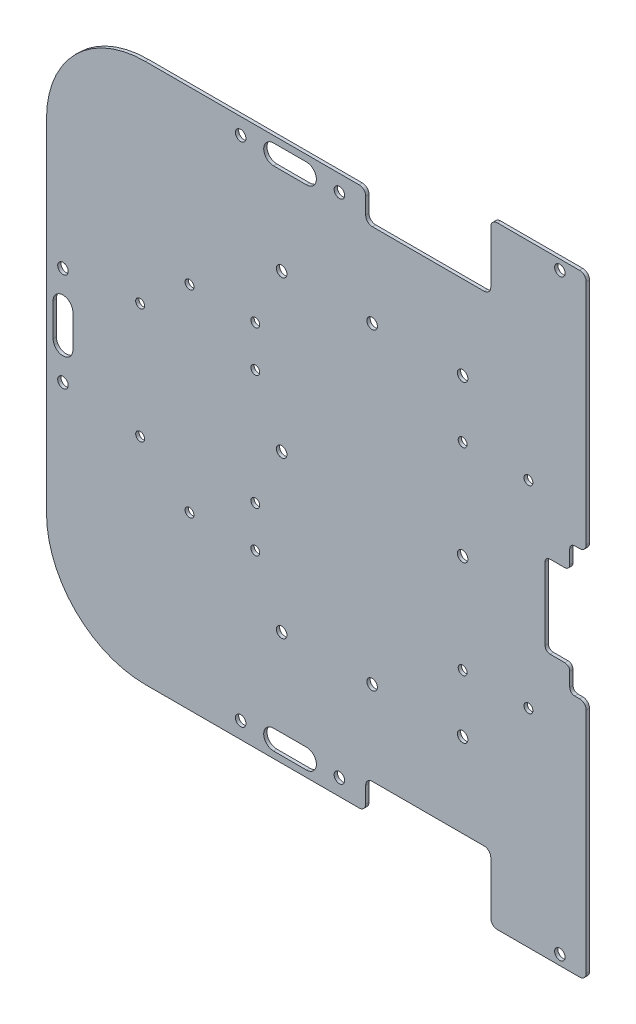
SolidWorks part; units mm, degrees
material "Thornel Mat VMA"
ref_plane "前视基准面" through (0, 0, 0) normal (0, 0, 1) x (1, 0, 0)
ref_plane "上视基准面" through (0, 0, 0) normal (0, 1, 0) x (1, 0, 0)
ref_plane "右视基准面" through (0, 0, 0) normal (1, 0, 0) x (0, 0, -1)
sketch "草图1" plane through (0, 0, 0) normal (0, 0, 1) x (1, 0, 0)
  line L1 (0, 0) -> (164, 0)
  line L2 (0, 0) -> (0, 164)
  line L3 (0, 164) -> (164, 164)
  line L4 (164, 0) -> (164, 164)
  dimension "D1" = 164
  dimension "D2" = 164
extrude "凸台-拉伸1" add sketch "草图1" along normal blind 1
fillet "圆角1" radius 30 2 edges at (0, 164, 0.5) (0, 0, 0.5)
sketch "草图2" plane through (0, 0, 1) normal (0, 0, 1) x (1, 0, 0)
  line L0 (0, 82) -> (245.8276, 82) construction
  line L1 (0, 134) -> (0, 30) construction
  line L2 (5, 77) -> (5, 87) construction
  line L3 (2, 77) -> (2, 87)
  line L4 (8, 77) -> (8, 87)
  circle A0 centre (5, 97) radius 1.6
  circle A1 centre (5, 87) radius 1.6 construction
  circle A2 centre (5, 77) radius 1.6 construction
  circle A3 centre (5, 67) radius 1.6
  arc A4 (2, 77) -> (8, 77) centre (5, 77) ccw
  arc A5 (8, 87) -> (2, 87) centre (5, 87) ccw
  point P8 (5, 82)
  dimension "D1" = 3.2
  dimension "D5" = 3
  dimension "D2" = 5
  dimension "D3" = 15
  dimension "D4" = 5
extrude "切除-拉伸1" cut sketch "草图2" against normal through all
sketch "草图3" plane through (0, 0, 1) normal (0, 0, 1) x (1, 0, 0)
  line L2 (0, 134) -> (0, 30) construction
  line L3 (59, 5) -> (69, 5) construction
  line L4 (30, 0) -> (164, 0) construction
  line L5 (0, 82) -> (216.0537, 82) construction
  line L6 (79, 5) -> (69, 5) construction
  line L7 (79, 2) -> (69, 2)
  line L8 (79, 8) -> (69, 8)
  line L9 (79, 159) -> (69, 159) construction
  line L10 (79, 162) -> (69, 162)
  line L11 (79, 156) -> (69, 156)
  circle A7 centre (59, 5) radius 1.6
  circle A8 centre (69, 5) radius 1.6 construction
  circle A9 centre (79, 5) radius 1.6 construction
  circle A10 centre (89, 5) radius 1.6
  circle A11 centre (89, 159) radius 1.6
  circle A12 centre (79, 159) radius 1.6 construction
  circle A13 centre (69, 159) radius 1.6 construction
  circle A14 centre (59, 159) radius 1.6
  arc A19 (79, 2) -> (79, 8) centre (79, 5) ccw
  arc A20 (69, 8) -> (69, 2) centre (69, 5) ccw
  arc A21 (79, 162) -> (79, 156) centre (79, 159) cw
  arc A22 (69, 156) -> (69, 162) centre (69, 159) cw
  point P24 (74, 5)
  point P26 (74, 159)
  dimension "D1" = 3.2
  dimension "D6" = 3
  dimension "D2" = 5
  dimension "D3" = 59
  dimension "D5" = 10
  dimension "D4" = 4
extrude "切除-拉伸2" cut sketch "草图3" against normal through all
sketch "草图4" plane through (0, 0, 1) normal (0, 0, 1) x (1, 0, 0)
  line L0 (0, 82) -> (207.5678, 82) construction
  line L2 (0, 134) -> (0, 30) construction
  line L4 (135, 155) -> (135, 164)
  line L5 (97, 155) -> (135, 155)
  line L6 (97, 0) -> (97, 9)
  line L7 (30, 0) -> (164, 0) construction
  line L8 (97, 9) -> (135, 9)
  line L9 (135, 9) -> (135, 0)
  line L10 (135, 0) -> (97, 0)
  line L12 (97, 164) -> (97, 155)
  line L13 (135, 164) -> (97, 164)
  dimension "D6" = 38
  dimension "D7" = 9
extrude "切除-拉伸3" cut sketch "草图4" against normal through all
sketch "草图5" plane through (164, 0, 0) normal (1, 0, 0) x (0, 0, -1)
  line L0 (0, 62.25) -> (-1, 62.25)
  line L1 (0, 0) -> (0, 164) construction
  line L2 (-1, 0) -> (-1, 164) construction
  line L3 (-1, 62.25) -> (-1, 71.75)
  line L4 (-1, 71.75) -> (0, 71.75)
  line L5 (0, 71.75) -> (0, 62.25)
  line L6 (-1, 82) -> (17.6584, 82) construction
  line L7 (-1, 92.25) -> (0, 92.25)
  line L8 (-1, 101.75) -> (-1, 92.25)
  line L9 (0, 101.75) -> (-1, 101.75)
  line L10 (0, 92.25) -> (0, 101.75)
  line L11 (-1, 67) -> (6.4031, 67) construction
  circle A3 centre (2, 67) radius 2.6 construction
  dimension "D2" = 5.2
  dimension "D1" = 15
  dimension "D3" = 3
  dimension "D4" = 9.5
extrude "切除-拉伸4" cut sketch "草图5" against normal blind 5
fillet "圆角3" radius 1.5 4 edges at (159, 62.25, 0.5) (159, 71.75, 0.5) (159, 92.25, 0.5) (159, 101.75, 0.5)
sketch "草图6" plane through (0, 0, 1) normal (0, 0, 1) x (1, 0, 0)
  line L0 (0, 82) -> (245.575, 82) construction
  line L1 (135, 164) -> (164, 164)
  line L2 (135, 164) -> (135, 175)
  line L3 (135, 175) -> (164, 175)
  line L4 (164, 164) -> (164, 175)
  line L5 (0, 134) -> (0, 30) construction
  line L6 (135, -11) -> (164, -11)
  line L7 (164, 0) -> (164, -11)
  line L8 (135, 0) -> (164, 0)
  line L9 (135, 0) -> (135, -11)
  line L10 (164, 101.75) -> (164, 164) construction
  dimension "D1" = 11
extrude "凸台-拉伸2" add sketch "草图6" against normal up to surface (1 mm away) up to face at (124.4743, 82, 0)
fillet "圆角2" radius 2 14 edges at (97, 155, 0.5) (97, 164, 0.5) (135, 155, 0.5) (135, 9, 0.5) (97, 9, 0.5) (97, 0, 0.5) (164, 101.75, 0.5) (164, 92.25, 0.5) (164, 71.75, 0.5) (164, 62.25, 0.5) (164, 175, 0.5) (135, 175, 0.5) (164, -11, 0.5) (135, -11, 0.5)
sketch "草图8" plane through (0, 0, 1) normal (0, 0, 1) x (1, 0, 0)
  line L0 (156, 177) -> (156, -47.5853) construction
  line L2 (164, 82) -> (50164, 82) construction
  line L3 (164, 103.75) -> (164, 173) construction
  line L5 (162, 175) -> (137, 175) construction
  line L6 (164, 73.75) -> (164, 90.25) construction
  circle A6 centre (156, 172) radius 1.6
  circle A8 centre (156, -8) radius 1.6
  point P13 (164, 82)
  dimension "D1" = 3.2
  dimension "D2" = 8
  dimension "D3" = 3
extrude "切除-拉伸5" cut sketch "草图8" against normal through all
sketch "草图9" plane through (0, 0, 0) normal (0, 0, -1) x (-1, 0, 0)
  line L0 (-85.8, 121.5) -> (-112.0984, 121.5) construction
  line L1 (-85.8, 121.5) -> (-112.0984, 121.5)
  line L24 (-20, -39.5) -> (-20, 9.1132)
  line L25 (-22.5, 13.4434) -> (-28.5, 16.9075)
  line L26 (-31, 21.2376) -> (-31, 142.7624)
  line L27 (-28.5, 147.0925) -> (-22.5, 150.5566)
  line L28 (-20, 154.8868) -> (-20, 203.5)
  line L29 (-25, 208.5) -> (-32.8, 208.5)
  line L30 (-34.3, 207) -> (-34.3, 204.5)
  line L31 (-34.3, 204.5) -> (-53.339, 204.5)
  line L32 (-56.3308, 203.5061) -> (-93.1692, 175.9939)
  line L33 (-96.161, 175) -> (-130, 175)
  line L34 (-135, 170) -> (-135, 157.8278)
  line L35 (-134.3412, 155.3471) -> (-116.4396, 124.0193)
  line L36 (-112.0984, 121.5) -> (-85.8, 121.5)
  line L37 (-80.8, 116.5) -> (-80.8, 47.5)
  line L38 (-85.8, 42.5) -> (-112.0984, 42.5)
  line L39 (-116.4396, 39.9807) -> (-134.3412, 8.6529)
  line L40 (-135, 6.1722) -> (-135, -6)
  line L41 (-130, -11) -> (-96.161, -11)
  line L42 (-93.1692, -11.9939) -> (-56.3308, -39.5061)
  line L43 (-53.339, -40.5) -> (-34.3, -40.5)
  line L44 (-34.3, -40.5) -> (-34.3, -43)
  line L45 (-32.8, -44.5) -> (-25, -44.5)
  line L46 (-20, -39.5) -> (-20, 9.1132)
  line L47 (-22.5, 13.4434) -> (-28.5, 16.9075)
  line L48 (-31, 21.2376) -> (-31, 142.7624)
  line L49 (-28.5, 147.0925) -> (-22.5, 150.5566)
  line L50 (-20, 154.8868) -> (-20, 203.5)
  line L51 (-25, 208.5) -> (-32.8, 208.5)
  line L52 (-34.3, 207) -> (-34.3, 204.5)
  line L53 (-34.3, 204.5) -> (-53.339, 204.5)
  line L54 (-56.3308, 203.5061) -> (-93.1692, 175.9939)
  line L55 (-96.161, 175) -> (-130, 175)
  line L56 (-135, 170) -> (-135, 157.8278)
  line L57 (-134.3412, 155.3471) -> (-116.4396, 124.0193)
  line L58 (-112.0984, 121.5) -> (-85.8, 121.5)
  line L59 (-80.8, 116.5) -> (-80.8, 47.5)
  line L60 (-85.8, 42.5) -> (-112.0984, 42.5)
  line L61 (-116.4396, 39.9807) -> (-134.3412, 8.6529)
  line L62 (-135, 6.1722) -> (-135, -6)
  line L63 (-130, -11) -> (-96.161, -11)
  line L64 (-93.1692, -11.9939) -> (-56.3308, -39.5061)
  line L65 (-53.339, -40.5) -> (-34.3, -40.5)
  line L66 (-34.3, -40.5) -> (-34.3, -43)
  line L67 (-32.8, -44.5) -> (-25, -44.5)
  parabola Q20 (-20, 9.1132) -> (-22.5, 13.4434) focus (-22.5, 10.5566) apex (-20.625, 11.6392)
  parabola Q21 (-28.5, 16.9075) -> (-31, 21.2376) focus (-28.5, 19.7942) apex (-30.375, 18.7117)
  parabola Q22 (-31, 142.7624) -> (-28.5, 147.0925) focus (-28.5, 144.2058) apex (-30.375, 145.2883)
  parabola Q23 (-22.5, 150.5566) -> (-20, 154.8868) focus (-22.5, 153.4434) apex (-20.625, 152.3608)
  parabola Q24 (-20, 203.5) -> (-25, 208.5) focus (-22.5, 206) apex (-21.25, 207.25)
  parabola Q25 (-32.8, 208.5) -> (-34.3, 207) focus (-33.55, 207.75) apex (-33.925, 208.125)
  parabola Q26 (-53.339, 204.5) -> (-56.3308, 203.5061) focus (-54.1695, 202) apex (-54.9175, 204.2515)
  parabola Q27 (-93.1692, 175.9939) -> (-96.161, 175) focus (-95.3305, 177.5) apex (-94.5825, 175.2485)
  parabola Q28 (-130, 175) -> (-135, 170) focus (-132.5, 172.5) apex (-133.75, 173.75)
  parabola Q29 (-135, 157.8278) -> (-134.3412, 155.3471) focus (-132.5, 157.1639) apex (-134.8353, 156.5437)
  parabola Q30 (-116.4396, 124.0193) -> (-112.0984, 121.5) focus (-113.5492, 124) apex (-114.6345, 122.1298)
  parabola Q31 (-85.8, 121.5) -> (-80.8, 116.5) focus (-83.3, 119) apex (-82.05, 120.25)
  parabola Q32 (-80.8, 47.5) -> (-85.8, 42.5) focus (-83.3, 45) apex (-82.05, 43.75)
  parabola Q33 (-112.0984, 42.5) -> (-116.4396, 39.9807) focus (-113.5492, 40) apex (-114.6345, 41.8702)
  parabola Q34 (-134.3412, 8.6529) -> (-135, 6.1722) focus (-132.5, 6.8361) apex (-134.8353, 7.4563)
  parabola Q35 (-135, -6) -> (-130, -11) focus (-132.5, -8.5) apex (-133.75, -9.75)
  parabola Q36 (-96.161, -11) -> (-93.1692, -11.9939) focus (-95.3305, -13.5) apex (-94.5825, -11.2485)
  parabola Q37 (-56.3308, -39.5061) -> (-53.339, -40.5) focus (-54.1695, -38) apex (-54.9175, -40.2515)
  parabola Q38 (-34.3, -43) -> (-32.8, -44.5) focus (-33.55, -43.75) apex (-33.925, -44.125)
  parabola Q39 (-25, -44.5) -> (-20, -39.5) focus (-22.5, -42) apex (-21.25, -43.25)
  parabola Q40 (-20, 9.1132) -> (-22.5, 13.4434) focus (-22.5, 10.5566) apex (-20.625, 11.6392)
  parabola Q41 (-28.5, 16.9075) -> (-31, 21.2376) focus (-28.5, 19.7942) apex (-30.375, 18.7117)
  parabola Q42 (-31, 142.7624) -> (-28.5, 147.0925) focus (-28.5, 144.2058) apex (-30.375, 145.2883)
  parabola Q43 (-22.5, 150.5566) -> (-20, 154.8868) focus (-22.5, 153.4434) apex (-20.625, 152.3608)
  parabola Q44 (-20, 203.5) -> (-25, 208.5) focus (-22.5, 206) apex (-21.25, 207.25)
  parabola Q45 (-32.8, 208.5) -> (-34.3, 207) focus (-33.55, 207.75) apex (-33.925, 208.125)
  parabola Q46 (-53.339, 204.5) -> (-56.3308, 203.5061) focus (-54.1695, 202) apex (-54.9175, 204.2515)
  parabola Q47 (-93.1692, 175.9939) -> (-96.161, 175) focus (-95.3305, 177.5) apex (-94.5825, 175.2485)
  parabola Q48 (-130, 175) -> (-135, 170) focus (-132.5, 172.5) apex (-133.75, 173.75)
  parabola Q49 (-135, 157.8278) -> (-134.3412, 155.3471) focus (-132.5, 157.1639) apex (-134.8353, 156.5437)
  parabola Q50 (-116.4396, 124.0193) -> (-112.0984, 121.5) focus (-113.5492, 124) apex (-114.6345, 122.1298)
  parabola Q51 (-85.8, 121.5) -> (-80.8, 116.5) focus (-83.3, 119) apex (-82.05, 120.25)
  parabola Q52 (-80.8, 47.5) -> (-85.8, 42.5) focus (-83.3, 45) apex (-82.05, 43.75)
  parabola Q53 (-112.0984, 42.5) -> (-116.4396, 39.9807) focus (-113.5492, 40) apex (-114.6345, 41.8702)
  parabola Q54 (-134.3412, 8.6529) -> (-135, 6.1722) focus (-132.5, 6.8361) apex (-134.8353, 7.4563)
  parabola Q55 (-135, -6) -> (-130, -11) focus (-132.5, -8.5) apex (-133.75, -9.75)
  parabola Q56 (-96.161, -11) -> (-93.1692, -11.9939) focus (-95.3305, -13.5) apex (-94.5825, -11.2485)
  parabola Q57 (-56.3308, -39.5061) -> (-53.339, -40.5) focus (-54.1695, -38) apex (-54.9175, -40.2515)
  parabola Q58 (-34.3, -43) -> (-32.8, -44.5) focus (-33.55, -43.75) apex (-33.925, -44.125)
  parabola Q59 (-25, -44.5) -> (-20, -39.5) focus (-22.5, -42) apex (-21.25, -43.25)
  dimension "D1" = 0
sketch "草图10" plane through (0, 0, 1) normal (0, 0, 1) x (1, 0, 0)
  line L0 (98.9492, 121.5) -> (98.9492, 42.5) construction
  line L1 (85.8, 121.5) -> (112.0984, 121.5) construction
  line L2 (85.8, 42.5) -> (112.0984, 42.5) construction
  line L3 (71.4492, 34.5) -> (126.4492, 34.5) construction
  line L4 (0, 82) -> (-50000, 82) construction
  line L5 (71.4492, 129.5) -> (126.4492, 129.5) construction
  line L6 (71.4492, 129.5) -> (71.4492, 34.5) construction
  line L7 (71.4492, 34.5) -> (126.4492, 34.5) construction
  line L8 (126.4492, 129.5) -> (126.4492, 34.5) construction
  line L9 (98.9492, 34.5) -> (98.9492, 129.5) construction
  line L10 (71.4492, 82) -> (126.4492, 82) construction
  line L11 (0, 134) -> (0, 30) construction
  line L13 (43.4492, 112) -> (63.4492, 112) construction
  line L14 (43.4492, 112) -> (43.4492, 52) construction
  line L15 (43.4492, 52) -> (63.4492, 52) construction
  line L16 (63.4492, 112) -> (63.4492, 52) construction
  line L17 (53.4492, 52) -> (53.4492, 112) construction
  line L18 (43.4492, 82) -> (63.4492, 82) construction
  line L19 (126.4492, 112) -> (146.4492, 112) construction
  line L20 (28.4492, 99.5) -> (63.4492, 99.5) construction
  line L21 (28.4492, 99.5) -> (28.4492, 64.5) construction
  line L22 (28.4492, 64.5) -> (63.4492, 64.5) construction
  line L23 (63.4492, 99.5) -> (63.4492, 64.5) construction
  line L24 (45.9492, 64.5) -> (45.9492, 99.5) construction
  line L25 (28.4492, 82) -> (63.4492, 82) construction
  line L26 (126.4492, 112) -> (126.4492, 52) construction
  line L27 (126.4492, 52) -> (146.4492, 52) construction
  line L28 (146.4492, 112) -> (146.4492, 52) construction
  line L29 (136.4492, 52) -> (136.4492, 112) construction
  line L30 (126.4492, 82) -> (146.4492, 82) construction
  circle A0 centre (71.4492, 129.5) radius 1.6
  circle A1 centre (98.9492, 129.5) radius 1.6
  circle A2 centre (126.4492, 129.5) radius 1.6
  circle A3 centre (71.4492, 82) radius 1.6
  circle A4 centre (126.4492, 34.5) radius 1.6
  circle A5 centre (98.9492, 34.5) radius 1.6
  circle A6 centre (71.4492, 34.5) radius 1.6
  circle A7 centre (126.4492, 82) radius 1.6
  circle A8 centre (28.4492, 99.5) radius 1.35
  circle A9 centre (63.4492, 99.5) radius 1.35
  circle A10 centre (63.4492, 64.5) radius 1.35
  circle A11 centre (28.4492, 64.5) radius 1.35
  circle A12 centre (146.4492, 112) radius 1.35
  circle A13 centre (43.4492, 112) radius 1.35
  circle A14 centre (63.4492, 112) radius 1.35
  circle A15 centre (63.4492, 52) radius 1.35
  circle A16 centre (43.4492, 52) radius 1.35
  circle A17 centre (126.4492, 112) radius 1.35
  circle A18 centre (146.4492, 52) radius 1.35
  circle A19 centre (126.4492, 52) radius 1.35
  point P2 (136.4492, 82)
  point P9 (98.9492, 82)
  point P26 (0, 82)
  point P27 (53.4492, 82)
  point P32 (45.9492, 82)
  dimension "D3" = 20
  dimension "3.2" = 3.2
  dimension "D7" = 20
  dimension "2.7" = 2.7
  dimension "D1" = 55
  dimension "D2" = 95
  dimension "D4" = 60
  dimension "D5" = 18
  dimension "D6" = 35
  dimension "D8" = 60
extrude "切除-拉伸6" cut sketch "草图10" against normal through all
sketch "草图12" plane through (0, 0, 1) normal (0, 0, 1) x (1, 0, 0)
  line L0 (159, 100.25) -> (159, 93.75) construction
  line L1 (159, 94.5) -> (151.5, 94.5)
  line L3 (159, 69.5) -> (151.5, 69.5)
  line L4 (151.5, 94.5) -> (151.5, 69.5)
  line L5 (151.5, 82) -> (0, 82) construction
  line L7 (159, 70.25) -> (159, 63.75) construction
  line L8 (0, 134) -> (0, 30) construction
  line L9 (160.5, 71.75) -> (162, 71.75) construction
  line L10 (164, 73.75) -> (164, 90.25) construction
  line L11 (160.5, 92.25) -> (162, 92.25) construction
  line L12 (159, 70.25) -> (159, 69.5)
  line L13 (160.5, 71.75) -> (162, 71.75)
  line L14 (164, 73.75) -> (164, 90.25)
  line L15 (160.5, 92.25) -> (162, 92.25)
  line L16 (159, 94.5) -> (159, 93.75)
  arc A0 (160.5, 71.75) -> (159, 70.25) centre (160.5, 70.25) ccw construction
  arc A1 (162, 71.75) -> (164, 73.75) centre (162, 73.75) ccw construction
  arc A2 (164, 90.25) -> (162, 92.25) centre (162, 90.25) ccw construction
  arc A3 (159, 93.75) -> (160.5, 92.25) centre (160.5, 93.75) ccw construction
  arc A4 (160.5, 71.75) -> (159, 70.25) centre (160.5, 70.25) ccw
  arc A5 (162, 71.75) -> (164, 73.75) centre (162, 73.75) ccw
  arc A6 (164, 90.25) -> (162, 92.25) centre (162, 90.25) ccw
  arc A7 (159, 93.75) -> (160.5, 92.25) centre (160.5, 93.75) ccw
  dimension "D1" = 7.5
  dimension "D2" = 25
extrude "切除-拉伸7" cut sketch "草图12" against normal through all
fillet "圆角4" radius 1.5 4 edges at (159, 69.5, 0.5) (151.5, 69.5, 0.5) (151.5, 94.5, 0.5) (159, 94.5, 0.5)
